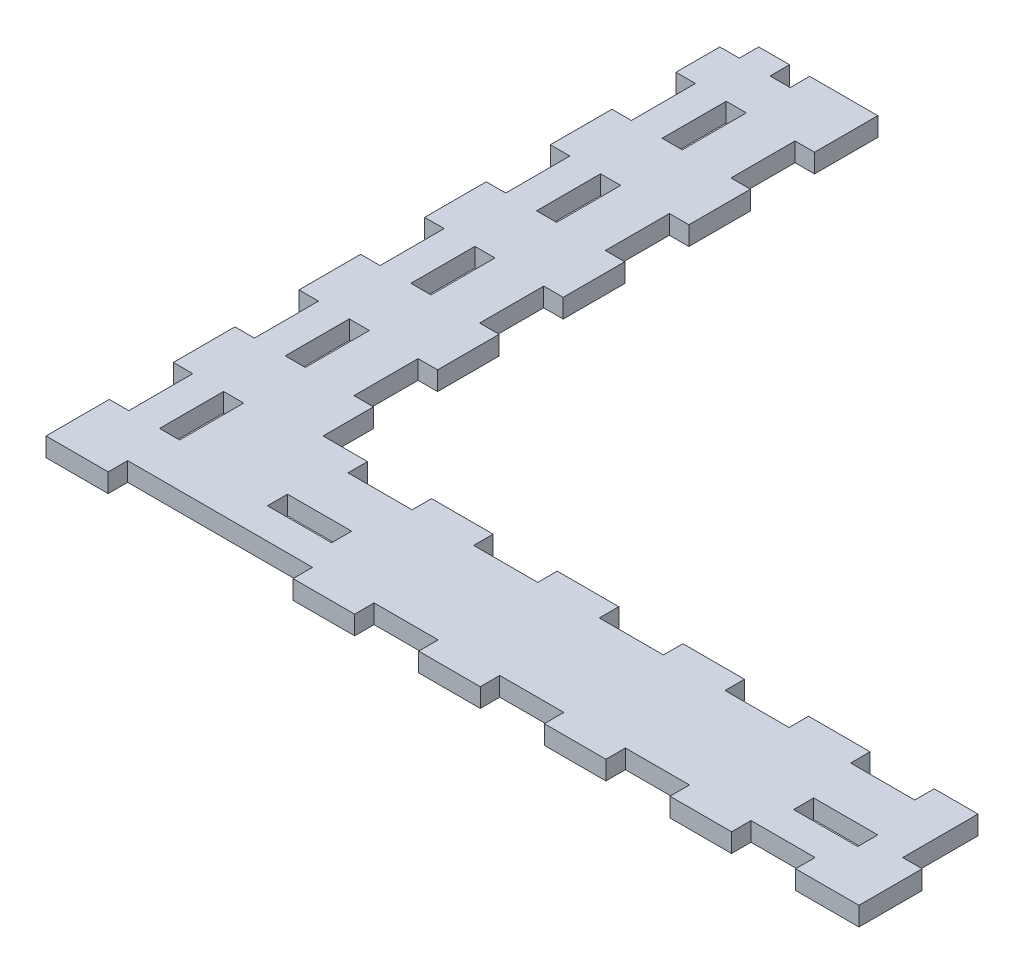
SolidWorks part; units mm, degrees
ref_plane "Front Plane" through (0, 0, 0) normal (0, 0, 1) x (1, 0, 0)
ref_plane "Top Plane" through (0, 0, 0) normal (0, 1, 0) x (1, 0, 0)
ref_plane "Right Plane" through (0, 0, 0) normal (1, 0, 0) x (0, 0, -1)
sketch "Sketch1" plane through (0, 0, 0) normal (0, 1, 0) x (1, 0, 0)
  line L0 (129.3944, 22.05) -> (22.05, 22.05)
  line L1 (0, 110.3444) -> (129.3944, 110.3444) construction
  line L2 (0, 110.3444) -> (0, 0)
  line L3 (0, 0) -> (129.3944, 0)
  line L4 (129.3944, 110.3444) -> (129.3944, 0) construction
  line L5 (22.05, 22.05) -> (22.05, 110.3444)
  line L6 (-40.65, 22.05) -> (69.6944, 22.05) construction
  line L7 (0, 110.3444) -> (22.05, 110.3444)
  line L8 (129.3944, 22.05) -> (129.3944, 0)
extrude "Boss-Extrude1" add sketch "Sketch1" against normal up to vertex (3 mm away)
sketch "Sketch2" plane through (0, 0, 0) normal (0, 1, 0) x (1, 0, 0)
  line L0 (39.2222, 3) -> (39.2222, 0)
  line L1 (19.05, 110.3444) -> (19.05, 0) construction
  line L2 (3, 110.3444) -> (3, 0) construction
  line L3 (11.1, 110.3444) -> (11.1, 0) construction
  line L4 (8.1, 110.3444) -> (8.1, 0) construction
  line L5 (0, 107.3444) -> (22.05, 107.3444) construction
  line L6 (129.3944, 22.05) -> (22.05, 22.05)
  line L7 (22.05, 22.05) -> (22.05, 110.3444)
  line L8 (22.05, 110.3444) -> (0, 110.3444)
  line L9 (0, 110.3444) -> (0, 0)
  line L10 (0, 0) -> (129.3944, 0)
  line L11 (129.3944, 0) -> (129.3944, 22.05)
  line L12 (129.3944, 22.05) -> (22.05, 22.05)
  line L13 (22.05, 22.05) -> (22.05, 110.3444)
  line L14 (22.05, 110.3444) -> (0, 110.3444)
  line L15 (0, 110.3444) -> (0, 0)
  line L16 (0, 0) -> (129.3944, 0)
  line L17 (129.3944, 0) -> (129.3944, 22.05)
  line L18 (0, 3) -> (129.3944, 3) construction
  line L19 (129.3944, 19.05) -> (19.05, 19.05) construction
  line L20 (126.3944, 22.05) -> (126.3944, 0) construction
  line L21 (119.2222, 19.05) -> (119.2222, 22.05) construction
  line L22 (109.2222, 19.05) -> (109.2222, 22.05) construction
  line L23 (99.2222, 19.05) -> (99.2222, 22.05) construction
  line L24 (89.2222, 19.05) -> (89.2222, 22.05) construction
  line L25 (79.2222, 19.05) -> (79.2222, 22.05) construction
  line L26 (69.2222, 19.05) -> (69.2222, 22.05) construction
  line L27 (59.2222, 19.05) -> (59.2222, 22.05) construction
  line L28 (49.2222, 19.05) -> (49.2222, 22.05) construction
  line L29 (39.2222, 19.05) -> (39.2222, 22.05) construction
  line L30 (29.2222, 19.05) -> (29.2222, 22.05) construction
  line L31 (10, 3) -> (10, 0)
  line L32 (74.2222, 0) -> (74.2222, 22.05) construction
  line L33 (19.05, 8.1) -> (129.3944, 8.1) construction
  line L34 (129.3944, 11.1) -> (19.05, 11.1) construction
  line L35 (111.0944, 8.1) -> (111.0944, 11.1)
  line L36 (121.0944, 8.1) -> (121.0944, 11.1)
  line L37 (37.35, 8.1) -> (37.35, 11.1)
  line L38 (27.35, 8.1) -> (27.35, 11.1)
  line L39 (49.2222, 3) -> (49.2222, 0)
  line L40 (59.2222, 3) -> (59.2222, 0)
  line L41 (69.2222, 3) -> (69.2222, 0)
  line L42 (119.2222, 3) -> (119.2222, 0)
  line L43 (109.2222, 3) -> (109.2222, 0)
  line L44 (99.2222, 3) -> (99.2222, 0)
  line L45 (89.2222, 3) -> (89.2222, 0)
  line L46 (79.2222, 3) -> (79.2222, 0)
  line L47 (19.05, 30.1722) -> (22.05, 30.1722)
  line L48 (19.05, 40.1722) -> (22.05, 40.1722)
  line L49 (19.05, 50.1722) -> (22.05, 50.1722)
  line L50 (19.05, 60.1722) -> (22.05, 60.1722)
  line L51 (19.05, 70.1722) -> (22.05, 70.1722)
  line L52 (19.05, 80.1722) -> (22.05, 80.1722)
  line L53 (19.05, 90.1722) -> (22.05, 90.1722)
  line L54 (19.05, 100.1722) -> (22.05, 100.1722)
  line L55 (11.1, 100.1722) -> (8.1, 100.1722)
  line L56 (11.1, 90.1722) -> (8.1, 90.1722)
  line L57 (11.1, 80.1722) -> (8.1, 80.1722)
  line L58 (11.1, 70.1722) -> (8.1, 70.1722)
  line L59 (11.1, 60.1722) -> (8.1, 60.1722)
  line L60 (11.1, 50.1722) -> (8.1, 50.1722)
  line L61 (11.1, 40.1722) -> (8.1, 40.1722)
  line L62 (11.1, 30.1722) -> (8.1, 30.1722)
  line L63 (11.1, 20.1722) -> (8.1, 20.1722)
  line L64 (11.1, 10.1722) -> (8.1, 10.1722)
  line L65 (3, 10.1722) -> (0, 10.1722)
  line L66 (3, 20.1722) -> (0, 20.1722)
  line L67 (3, 100.1722) -> (0, 100.1722)
  line L68 (3, 90.1722) -> (0, 90.1722)
  line L69 (3, 80.1722) -> (0, 80.1722)
  line L70 (3, 70.1722) -> (0, 70.1722)
  line L71 (3, 60.1722) -> (0, 60.1722)
  line L72 (3, 50.1722) -> (0, 50.1722)
  line L73 (3, 40.1722) -> (0, 40.1722)
  line L74 (3, 30.1722) -> (0, 30.1722)
  line L75 (1.5, 10.1722) -> (1.5, 20.1722) construction
  line L76 (1.5, 20.1722) -> (1.5, 30.1722) construction
  line L77 (1.5, 30.1722) -> (1.5, 40.1722) construction
  line L78 (3, 107.3444) -> (0, 107.3444)
  line L79 (11.1, 107.3444) -> (8.1, 107.3444)
  dimension "D1" = 0
sketch "Sketch4" plane through (0, 0, 0) normal (0, 1, 0) x (1, 0, 0)
  line L0 (74.2222, 0) -> (74.2222, 22.05) construction
  line L1 (49.1222, 22.15) -> (59.3222, 22.15)
  line L2 (49.1222, 22.15) -> (49.1222, 18.95)
  line L3 (49.1222, 18.95) -> (59.3222, 18.95)
  line L4 (59.3222, 22.15) -> (59.3222, 18.95)
  line L5 (69.1222, 22.15) -> (79.3222, 22.15)
  line L6 (69.1222, 22.15) -> (69.1222, 18.95)
  line L7 (69.1222, 18.95) -> (79.3222, 18.95)
  line L8 (79.3222, 22.15) -> (79.3222, 18.95)
  line L9 (74.2222, 0) -> (74.2222, 22.05) construction
  line L10 (29.2222, 19.05) -> (29.3222, 19.05) construction
  line L11 (109.1222, 3.1) -> (119.3222, 3.1)
  line L12 (109.1222, 3.1) -> (109.1222, -0.1)
  line L13 (109.1222, -0.1) -> (119.3222, -0.1)
  line L14 (119.3222, 3.1) -> (119.3222, -0.1)
  line L15 (-0.1, 20.2722) -> (3.1, 20.2722)
  line L16 (-0.1, 20.2722) -> (-0.1, 10.0722)
  line L17 (39.3222, 22.15) -> (29.1222, 22.15)
  line L18 (39.3222, 22.15) -> (39.3222, 18.95)
  line L19 (39.3222, 18.95) -> (29.1222, 18.95)
  line L20 (29.1222, 22.15) -> (29.1222, 18.95)
  line L21 (9.9, 3.1) -> (39.3222, 3.1)
  line L22 (9.9, 3.1) -> (9.9, -0.1)
  line L23 (9.9, -0.1) -> (39.3222, -0.1)
  line L24 (39.3222, 3.1) -> (39.3222, -0.1)
  line L25 (27.25, 11.2) -> (37.45, 11.2)
  line L26 (27.25, 11.2) -> (27.25, 8)
  line L27 (27.25, 8) -> (37.45, 8)
  line L28 (37.45, 11.2) -> (37.45, 8)
  line L29 (49.1222, 3.1) -> (59.3222, 3.1)
  line L30 (49.1222, 3.1) -> (49.1222, -0.1)
  line L31 (49.1222, -0.1) -> (59.3222, -0.1)
  line L32 (59.3222, 3.1) -> (59.3222, -0.1)
  line L33 (69.1222, 3.1) -> (79.3222, 3.1)
  line L34 (69.1222, 3.1) -> (69.1222, -0.1)
  line L35 (69.1222, -0.1) -> (79.3222, -0.1)
  line L36 (79.3222, 3.1) -> (79.3222, -0.1)
  line L37 (-0.1, 10.0722) -> (3.1, 10.0722)
  line L38 (3.1, 20.2722) -> (3.1, 10.0722)
  line L39 (8, 20.2722) -> (11.2, 20.2722)
  line L40 (8, 20.2722) -> (8, 10.0722)
  line L41 (8, 10.0722) -> (11.2, 10.0722)
  line L42 (11.2, 20.2722) -> (11.2, 10.0722)
  line L43 (3.1, 30.0722) -> (-0.1, 30.0722)
  line L44 (3.1, 30.0722) -> (3.1, 40.2722)
  line L45 (3.1, 40.2722) -> (-0.1, 40.2722)
  line L46 (-0.1, 30.0722) -> (-0.1, 40.2722)
  line L47 (8, 40.2722) -> (11.2, 40.2722)
  line L48 (8, 40.2722) -> (8, 30.0722)
  line L49 (8, 30.0722) -> (11.2, 30.0722)
  line L50 (11.2, 40.2722) -> (11.2, 30.0722)
  line L51 (18.95, 40.2722) -> (22.15, 40.2722)
  line L52 (18.95, 40.2722) -> (18.95, 30.0722)
  line L53 (18.95, 30.0722) -> (22.15, 30.0722)
  line L54 (22.15, 40.2722) -> (22.15, 30.0722)
  line L55 (-0.1, 110.4444) -> (3.1, 110.4444)
  line L56 (-0.1, 110.4444) -> (-0.1, 107.2444)
  line L57 (-0.1, 107.2444) -> (3.1, 107.2444)
  line L58 (3.1, 110.4444) -> (3.1, 107.2444)
  line L59 (8, 110.4444) -> (11.2, 110.4444)
  line L60 (8, 110.4444) -> (8, 107.2444)
  line L61 (8, 107.2444) -> (11.2, 107.2444)
  line L62 (11.2, 110.4444) -> (11.2, 107.2444)
  line L63 (8, 100.2722) -> (11.2, 100.2722)
  line L64 (8, 100.2722) -> (8, 90.0722)
  line L65 (8, 90.0722) -> (11.2, 90.0722)
  line L66 (11.2, 100.2722) -> (11.2, 90.0722)
  line L67 (-0.1, 100.2722) -> (3.1, 100.2722)
  line L68 (-0.1, 100.2722) -> (-0.1, 90.0722)
  line L69 (-0.1, 90.0722) -> (3.1, 90.0722)
  line L70 (3.1, 100.2722) -> (3.1, 90.0722)
  line L71 (-0.1, 80.2722) -> (3.1, 80.2722)
  line L72 (-0.1, 80.2722) -> (-0.1, 70.0722)
  line L73 (-0.1, 70.0722) -> (3.1, 70.0722)
  line L74 (3.1, 80.2722) -> (3.1, 70.0722)
  line L75 (8, 80.2722) -> (11.2, 80.2722)
  line L76 (8, 80.2722) -> (8, 70.0722)
  line L77 (8, 70.0722) -> (11.2, 70.0722)
  line L78 (11.2, 80.2722) -> (11.2, 70.0722)
  line L79 (18.95, 100.2722) -> (22.15, 100.2722)
  line L80 (18.95, 100.2722) -> (18.95, 90.0722)
  line L81 (18.95, 90.0722) -> (22.15, 90.0722)
  line L82 (22.15, 100.2722) -> (22.15, 90.0722)
  line L83 (18.95, 80.2722) -> (22.15, 80.2722)
  line L84 (18.95, 80.2722) -> (18.95, 70.0722)
  line L85 (18.95, 70.0722) -> (22.15, 70.0722)
  line L86 (22.15, 80.2722) -> (22.15, 70.0722)
  line L87 (-0.1, 60.2722) -> (3.1, 60.2722)
  line L88 (-0.1, 60.2722) -> (-0.1, 50.0722)
  line L89 (-0.1, 50.0722) -> (3.1, 50.0722)
  line L90 (3.1, 60.2722) -> (3.1, 50.0722)
  line L91 (8, 60.2722) -> (11.2, 60.2722)
  line L92 (8, 60.2722) -> (8, 50.0722)
  line L93 (8, 50.0722) -> (11.2, 50.0722)
  line L94 (11.2, 60.2722) -> (11.2, 50.0722)
  line L95 (18.95, 60.2722) -> (22.15, 60.2722)
  line L96 (18.95, 60.2722) -> (18.95, 50.0722)
  line L97 (18.95, 50.0722) -> (22.15, 50.0722)
  line L98 (22.15, 60.2722) -> (22.15, 50.0722)
  line L99 (126.2944, 10.0722) -> (129.4944, 10.0722)
  line L100 (126.2944, 10.0722) -> (126.2944, 22.15)
  line L101 (126.2944, 22.15) -> (129.4944, 22.15)
  line L102 (129.4944, 10.0722) -> (129.4944, 22.15)
  line L103 (29.3222, 19.05) -> (29.3222, 18.95) construction
  line L104 (29.2222, 19.05) -> (29.1222, 19.05) construction
  line L105 (39.2222, 22.05) -> (39.3222, 22.05) construction
  line L106 (39.2222, 22.05) -> (39.2222, 22.15) construction
  line L107 (49.2222, 22.05) -> (49.1222, 22.05) construction
  line L108 (59.2222, 22.05) -> (59.3222, 22.05) construction
  line L109 (69.2222, 22.05) -> (69.1222, 22.05) construction
  line L110 (27.35, 11.1) -> (27.35, 11.2) construction
  line L111 (27.35, 11.1) -> (27.25, 11.1) construction
  line L112 (37.35, 8.1) -> (37.35, 8) construction
  line L113 (37.35, 8.1) -> (37.45, 8.1) construction
  line L114 (10, 0) -> (10, -0.1) construction
  line L115 (10, 0) -> (9.9, 0) construction
  line L116 (0, 0) -> (129.3944, 0) construction
  line L117 (39.2222, 3) -> (39.2222, 3.1) construction
  line L118 (119.2222, 0) -> (119.3222, 0) construction
  line L119 (99.3222, 3.1) -> (99.3222, -0.1)
  line L120 (99.3222, -0.1) -> (89.1222, -0.1)
  line L121 (89.1222, 3.1) -> (89.1222, -0.1)
  line L122 (99.3222, 3.1) -> (89.1222, 3.1)
  line L123 (109.1222, 22.15) -> (109.1222, 18.95)
  line L124 (109.1222, 18.95) -> (119.3222, 18.95)
  line L125 (119.3222, 22.15) -> (119.3222, 18.95)
  line L126 (109.1222, 22.15) -> (119.3222, 22.15)
  line L127 (99.3222, 22.15) -> (99.3222, 18.95)
  line L128 (99.3222, 22.15) -> (89.1222, 22.15)
  line L129 (89.1222, 22.15) -> (89.1222, 18.95)
  line L130 (99.3222, 18.95) -> (89.1222, 18.95)
  line L131 (119.2222, 3) -> (119.2222, 0) construction
  line L132 (121.1944, 11.2) -> (121.1944, 8)
  line L133 (121.1944, 8) -> (110.9944, 8)
  line L134 (110.9944, 11.2) -> (110.9944, 8)
  line L135 (121.1944, 11.2) -> (110.9944, 11.2)
  line L136 (0, 10.1722) -> (0, 10.0722) construction
  line L137 (0, 10.1722) -> (-0.1, 10.1722) construction
  line L138 (3, 10.1722) -> (3.1, 10.1722) construction
  line L139 (8.1, 10.1722) -> (8, 10.1722) construction
  line L140 (11.1, 10.1722) -> (11.2, 10.1722) construction
  line L141 (126.3944, 11.1) -> (126.2944, 11.1) construction
  line L142 (126.3944, 22.05) -> (126.3944, 0) construction
  line L143 (129.3944, 11.1) -> (19.05, 11.1) construction
  line L144 (19.05, 30.1722) -> (18.95, 30.1722) construction
  line L145 (19.05, 30.1722) -> (19.05, 30.0722) construction
  line L146 (22.05, 40.1722) -> (22.15, 40.1722) construction
  line L147 (22.05, 40.1722) -> (22.05, 40.2722) construction
  line L148 (11.1, 20.1722) -> (11.1, 20.2722) construction
  line L149 (0, 110.3444) -> (0, 110.4444) construction
  line L150 (0, 107.3444) -> (0, 107.2444) construction
  line L151 (0, 100.1722) -> (0, 100.2722) construction
  line L152 (0, 90.1722) -> (0, 90.0722) construction
  line L153 (0, 80.1722) -> (0, 80.2722) construction
  line L154 (0, 70.1722) -> (0, 70.0722) construction
  line L155 (0, 60.1722) -> (0, 60.2722) construction
  line L156 (0, 50.1722) -> (0, 50.0722) construction
  line L157 (129.3944, 11.1) -> (129.4944, 11.1) construction
extrude "Cut-Extrude1" cut sketch "Sketch4" against normal through all
